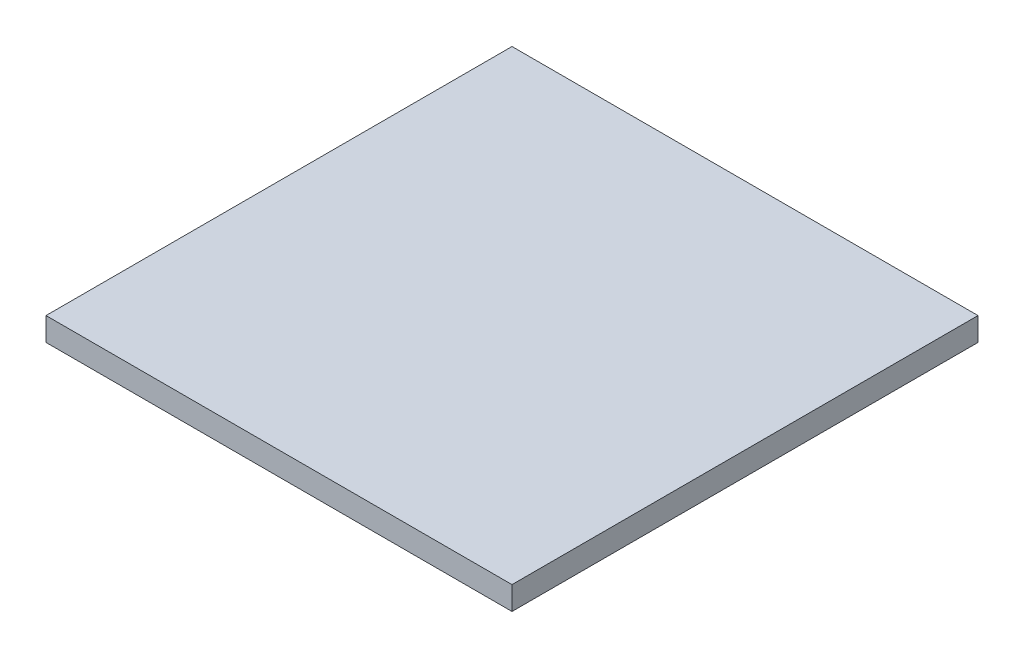
SolidWorks part; units mm, degrees
ref_plane "Front Plane" through (0, 0, 0) normal (0, 0, 1) x (1, 0, 0)
ref_plane "Top Plane" through (0, 0, 0) normal (0, 1, 0) x (1, 0, 0)
ref_plane "Right Plane" through (0, 0, 0) normal (1, 0, 0) x (0, 0, -1)
sketch "Sketch1" plane through (0, 0, 0) normal (0, 1, 0) x (1, 0, 0)
  line L1 (-104.4983, 61.2457) -> (95.5017, 61.2457)
  line L2 (-104.4983, 61.2457) -> (-104.4983, -138.7543)
  line L3 (-104.4983, -138.7543) -> (95.5017, -138.7543)
  line L4 (95.5017, 61.2457) -> (95.5017, -138.7543)
  dimension "D1" = 200
  dimension "D2" = 200
extrude "Boss-Extrude1" add sketch "Sketch1" along normal blind 10
